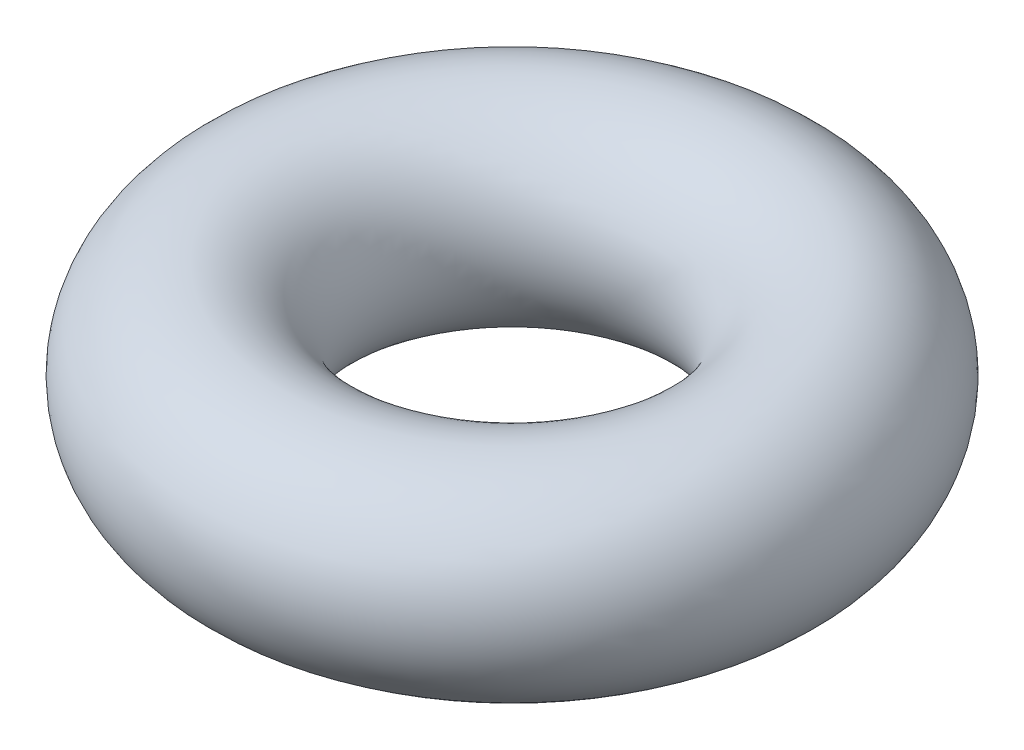
SolidWorks part; units mm, degrees
material "Natural Rubber"
ref_plane "Front Plane" through (0, 0, 0) normal (0, 0, 1) x (1, 0, 0)
ref_plane "Top Plane" through (0, 0, 0) normal (0, 1, 0) x (1, 0, 0)
ref_plane "Right Plane" through (0, 0, 0) normal (1, 0, 0) x (0, 0, -1)
sketch "Sketch1" plane through (0, 0, 0) normal (0, 0, 1) x (1, 0, 0)
  line L0 (0, 1.6918) -> (0, -1.2617) construction
  circle A0 centre (2.3622, 0) radius 1.016
  point P2 (1.3462, 0)
  dimension "D1" = 1.3462
  dimension "D2" = 2.032
revolve "Revolve1" add sketch "Sketch1" angle 360 about L0
